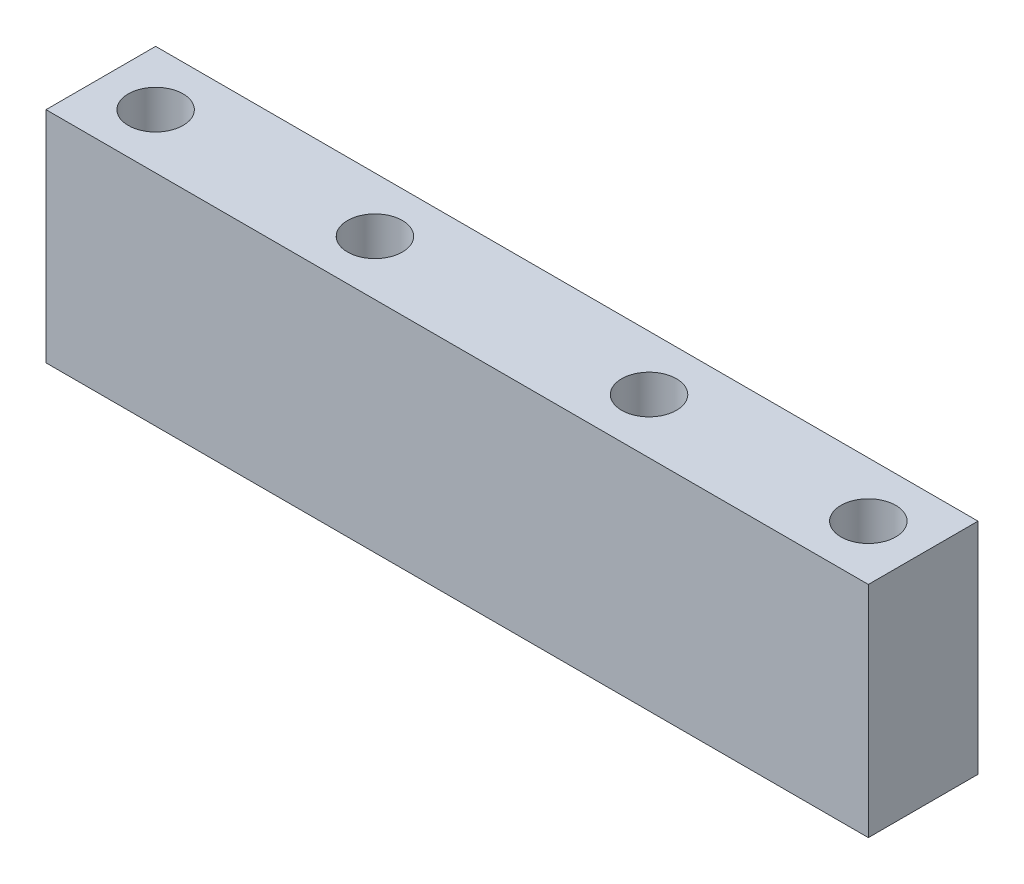
SolidWorks part; units mm, degrees
material "Delrin 2700 NC010, Low Viscosity Acetal Copolymer (SS)"
ref_plane "Front" through (0, 0, 0) normal (0, 0, 1) x (1, 0, 0)
ref_plane "Top" through (0, 0, 0) normal (0, 1, 0) x (1, 0, 0)
ref_plane "Right" through (0, 0, 0) normal (1, 0, 0) x (0, 0, -1)
sketch "Sketch1" plane through (0, 0, 0) normal (0, 1, 0) x (1, 0, 0)
  line L0 (41.275, 0) -> (-41.275, 0) construction
  line L2 (-47.625, 6.35) -> (47.625, 6.35)
  line L3 (-47.625, 6.35) -> (-47.625, -6.35)
  line L4 (-47.625, -6.35) -> (47.625, -6.35)
  line L5 (47.625, 6.35) -> (47.625, -6.35)
  circle A0 centre (-41.275, 0) radius 3.175
  circle A1 centre (41.275, 0) radius 3.175
  circle A3 centre (-15.875, 0) radius 3.175
  circle A4 centre (15.875, 0) radius 3.175
  point P4 (0, 0)
  point P11 (-47.625, 0)
  point P12 (0, 6.35)
  dimension "D2" = 6.35
  dimension "D1" = 82.55
  dimension "D3" = 12.7
  dimension "D4" = 95.25
  dimension "D5" = 25.4
  dimension "D6" = 25.4
extrude "Boss-Extrude1" add sketch "Sketch1" along normal blind 25.4
